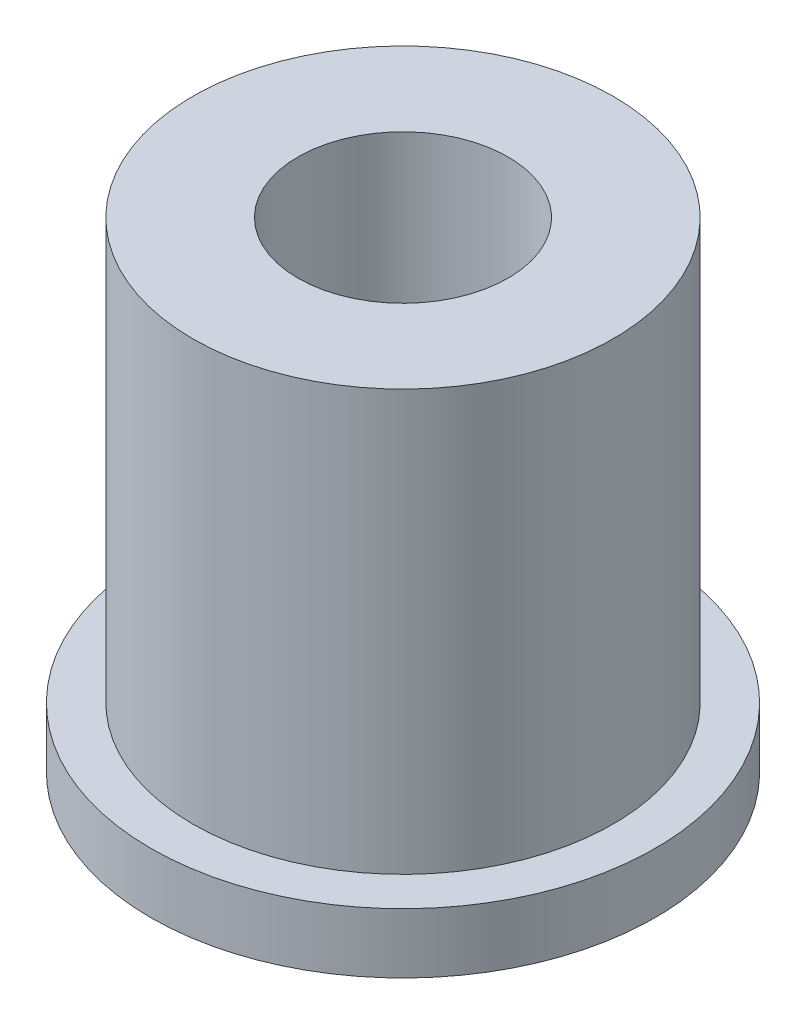
SolidWorks part; units mm, degrees
material "Chrome Stainless Steel"
ref_plane "Front" through (0, 0, 0) normal (0, 0, 1) x (1, 0, 0)
ref_plane "Top" through (0, 0, 0) normal (0, 1, 0) x (1, 0, 0)
ref_plane "Right" through (0, 0, 0) normal (1, 0, 0) x (0, 0, -1)
sketch "Sketch1" plane through (0, 0, 0) normal (0, 1, 0) x (1, 0, 0)
  circle A0 centre (0, 0) radius 21
  circle A1 centre (0, 0) radius 8.75
  dimension "D1" = 17.5
  dimension "D2" = 42
extrude "Boss-Extrude1" add sketch "Sketch1" along normal blind 5
sketch "Sketch2" plane through (0, 0, 0) normal (0, -1, 0) x (1, 0, 0)
  line L0 (-10.253, 10.253) -> (0, 0) construction
  line L1 (0, 0) -> (10.253, -10.253) construction
  line L2 (-14.5, 0) -> (14.5, 0) construction
  line L3 (8.8388, 8.8388) -> (0, 0) construction
  line L4 (0, 0) -> (-10.6066, -10.6066) construction
  line L5 (0, 0) -> (-8.8388, -8.8388) construction
  circle A0 centre (0, 0) radius 14.5 construction
  circle A1 centre (-10.253, 10.253) radius 2.1
  circle A2 centre (10.253, -10.253) radius 2.1
  circle A3 centre (0, 0) radius 15 construction
  circle A4 centre (-15, 0) radius 1.6
  circle A5 centre (7.5, 12.9904) radius 1.6
  circle A6 centre (7.5, -12.9904) radius 1.6
  circle A7 centre (0, 0) radius 12.5 construction
  circle A8 centre (8.8388, 8.8388) radius 1.6
  circle A9 centre (-8.8388, -8.8388) radius 1.6
  point P19 (0, 0)
  dimension "D1" = 45
  dimension "D2" = 4.2
  dimension "D3" = 30
  dimension "D4" = 3.2
  dimension "D6" = 25
  dimension "D7" = 45
  dimension "D8" = 3.2
  dimension "D5" = 3
extrude "Cut-Extrude1" cut sketch "Sketch2" against normal blind 5
sketch "Sketch3" plane through (0, 5, 0) normal (0, 1, 0) x (1, 0, 0)
  circle A0 centre (0, 0) radius 17.5
  circle A1 centre (0, 0) radius 8.75
  dimension "D1" = 35
extrude "Boss-Extrude2" add sketch "Sketch3" along normal blind 35
sketch "Sketch5" plane through (0, 5, 0) normal (0, 1, 0) x (1, 0, 0)
  circle A0 centre (0, 0) radius 21 construction
  point P0 (-21, 0)
